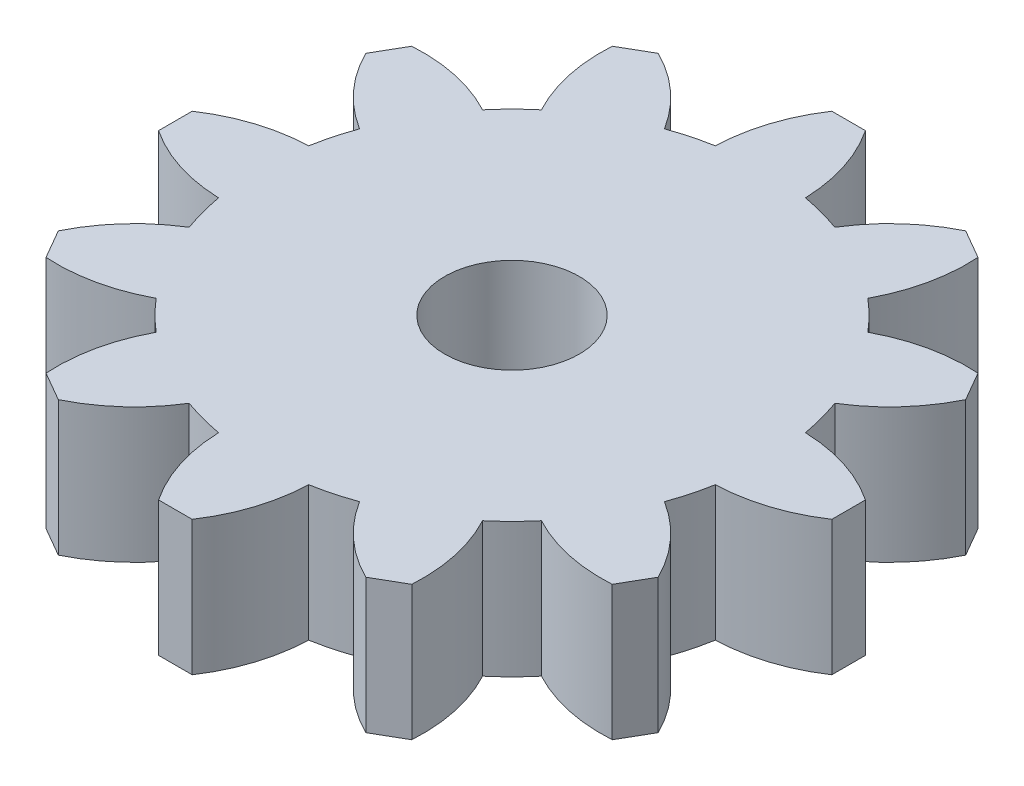
SolidWorks part; units mm, degrees
ref_plane "Front Plane" through (0, 0, 0) normal (0, 0, 1) x (1, 0, 0)
ref_plane "Top Plane" through (0, 0, 0) normal (0, 1, 0) x (1, 0, 0)
ref_plane "Right Plane" through (0, 0, 0) normal (1, 0, 0) x (0, 0, -1)
sketch "Sketch1" plane through (0, 0, 0) normal (0, 1, 0) x (1, 0, 0)
  line L0 (0, 0) -> (0, 25.6471) construction
  line L1 (-1, 20) -> (1, 20)
  line L2 (9.134, 17.8205) -> (10.866, 16.8205)
  line L3 (16.8205, 10.866) -> (17.8205, 9.134)
  line L4 (20, 1) -> (20, -1)
  line L5 (17.8205, -9.134) -> (16.8205, -10.866)
  line L6 (10.866, -16.8205) -> (9.134, -17.8205)
  line L7 (1, -20) -> (-1, -20)
  line L8 (-9.134, -17.8205) -> (-10.866, -16.8205)
  line L9 (-16.8205, -10.866) -> (-17.8205, -9.134)
  line L10 (-20, -1) -> (-20, 1)
  line L11 (-17.8205, 9.134) -> (-16.8205, 10.866)
  line L12 (-10.866, 16.8205) -> (-9.134, 17.8205)
  circle A0 centre (0, 0) radius 4
  arc A1 (-2.675, 14.7596) -> (-5.0632, 14.1196) centre (0, 0) ccw
  arc A2 (-1, 20) -> (-2.675, 14.7596) centre (7.3203, 14.4527) ccw
  arc A3 (1, 20) -> (2.675, 14.7596) centre (-7.3203, 14.4527) cw
  arc A4 (9.134, 17.8205) -> (5.0632, 14.1196) centre (13.5659, 8.8562) ccw
  arc A5 (10.866, 16.8205) -> (9.6964, 11.4446) centre (0.8868, 16.1765) cw
  arc A6 (16.8205, 10.866) -> (11.4446, 9.6964) centre (16.1765, 0.8868) ccw
  arc A7 (17.8205, 9.134) -> (14.1196, 5.0632) centre (8.8562, 13.5659) cw
  arc A8 (20, 1) -> (14.7596, 2.675) centre (14.4527, -7.3203) ccw
  arc A9 (20, -1) -> (14.7596, -2.675) centre (14.4527, 7.3203) cw
  arc A10 (17.8205, -9.134) -> (14.1196, -5.0632) centre (8.8562, -13.5659) ccw
  arc A11 (16.8205, -10.866) -> (11.4446, -9.6964) centre (16.1765, -0.8868) cw
  arc A12 (10.866, -16.8205) -> (9.6964, -11.4446) centre (0.8868, -16.1765) ccw
  arc A13 (9.134, -17.8205) -> (5.0632, -14.1196) centre (13.5659, -8.8562) cw
  arc A14 (1, -20) -> (2.675, -14.7596) centre (-7.3203, -14.4527) ccw
  arc A15 (-1, -20) -> (-2.675, -14.7596) centre (7.3203, -14.4527) cw
  arc A16 (-9.134, -17.8205) -> (-5.0632, -14.1196) centre (-13.5659, -8.8562) ccw
  arc A17 (-10.866, -16.8205) -> (-9.6964, -11.4446) centre (-0.8868, -16.1765) cw
  arc A18 (-16.8205, -10.866) -> (-11.4446, -9.6964) centre (-16.1765, -0.8868) ccw
  arc A19 (-17.8205, -9.134) -> (-14.1196, -5.0632) centre (-8.8562, -13.5659) cw
  arc A20 (-20, -1) -> (-14.7596, -2.675) centre (-14.4527, 7.3203) ccw
  arc A21 (-20, 1) -> (-14.7596, 2.675) centre (-14.4527, -7.3203) cw
  arc A22 (-17.8205, 9.134) -> (-14.1196, 5.0632) centre (-8.8562, 13.5659) ccw
  arc A23 (-16.8205, 10.866) -> (-11.4446, 9.6964) centre (-16.1765, 0.8868) cw
  arc A24 (-10.866, 16.8205) -> (-9.6964, 11.4446) centre (-0.8868, 16.1765) ccw
  arc A25 (-9.134, 17.8205) -> (-5.0632, 14.1196) centre (-13.5659, 8.8562) cw
  arc A26 (-9.6964, 11.4446) -> (-11.4446, 9.6964) centre (0, 0) ccw
  arc A27 (5.0632, 14.1196) -> (2.675, 14.7596) centre (0, 0) ccw
  arc A28 (11.4446, 9.6964) -> (9.6964, 11.4446) centre (0, 0) ccw
  arc A29 (14.7596, 2.675) -> (14.1196, 5.0632) centre (0, 0) ccw
  arc A30 (14.1196, -5.0632) -> (14.7596, -2.675) centre (0, 0) ccw
  arc A31 (9.6964, -11.4446) -> (11.4446, -9.6964) centre (0, 0) ccw
  arc A32 (2.675, -14.7596) -> (5.0632, -14.1196) centre (0, 0) ccw
  arc A33 (-5.0632, -14.1196) -> (-2.675, -14.7596) centre (0, 0) ccw
  arc A34 (-11.4446, -9.6964) -> (-9.6964, -11.4446) centre (0, 0) ccw
  arc A35 (-14.7596, -2.675) -> (-14.1196, -5.0632) centre (0, 0) ccw
  arc A36 (-14.1196, 5.0632) -> (-14.7596, 2.675) centre (0, 0) ccw
  point P9 (0, 20)
  point P81 (0, 0)
  dimension "D1" = 30
  dimension "D2" = 8
  dimension "D5" = 10
  dimension "D3" = 2
  dimension "D4" = 20
  dimension "D6" = 5.35
  dimension "D7" = 12
extrude "Boss-Extrude1" add sketch "Sketch1" along normal mid plane 8
